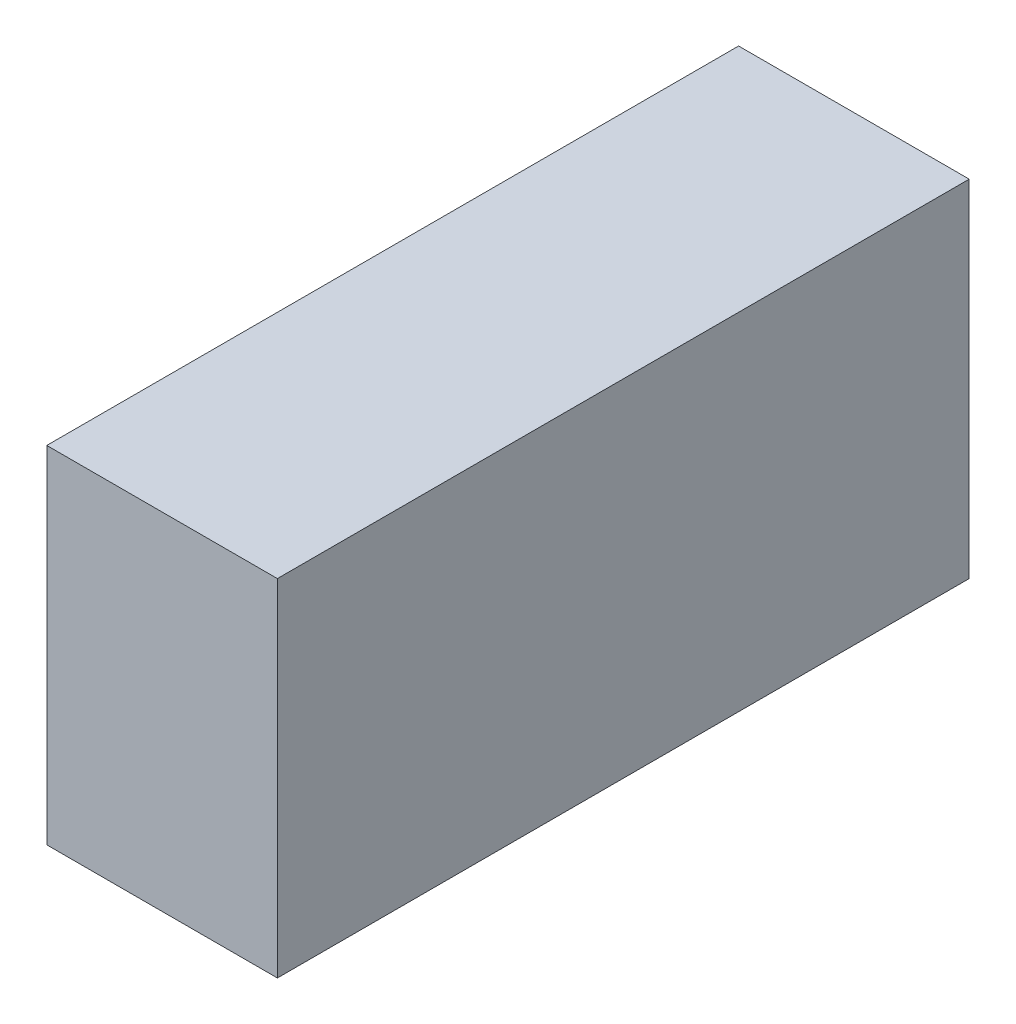
SolidWorks part; units mm, degrees
ref_plane "Front Plane" through (0, 0, 0) normal (0, 0, 1) x (1, 0, 0)
ref_plane "Top Plane" through (0, 0, 0) normal (0, 1, 0) x (1, 0, 0)
ref_plane "Right Plane" through (0, 0, 0) normal (1, 0, 0) x (0, 0, -1)
sketch "Sketch1" plane through (0, 0, 0) normal (0, 0, 1) x (1, 0, 0)
  line L5 (-20, 60) -> (20, 60)
  line L6 (-20, 60) -> (-20, 0)
  line L7 (-20, 0) -> (20, 0)
  line L8 (20, 60) -> (20, 0)
  dimension "D1" = 60
  dimension "D2" = 40
extrude "Boss-Extrude1" add sketch "Sketch1" along normal mid plane 120
